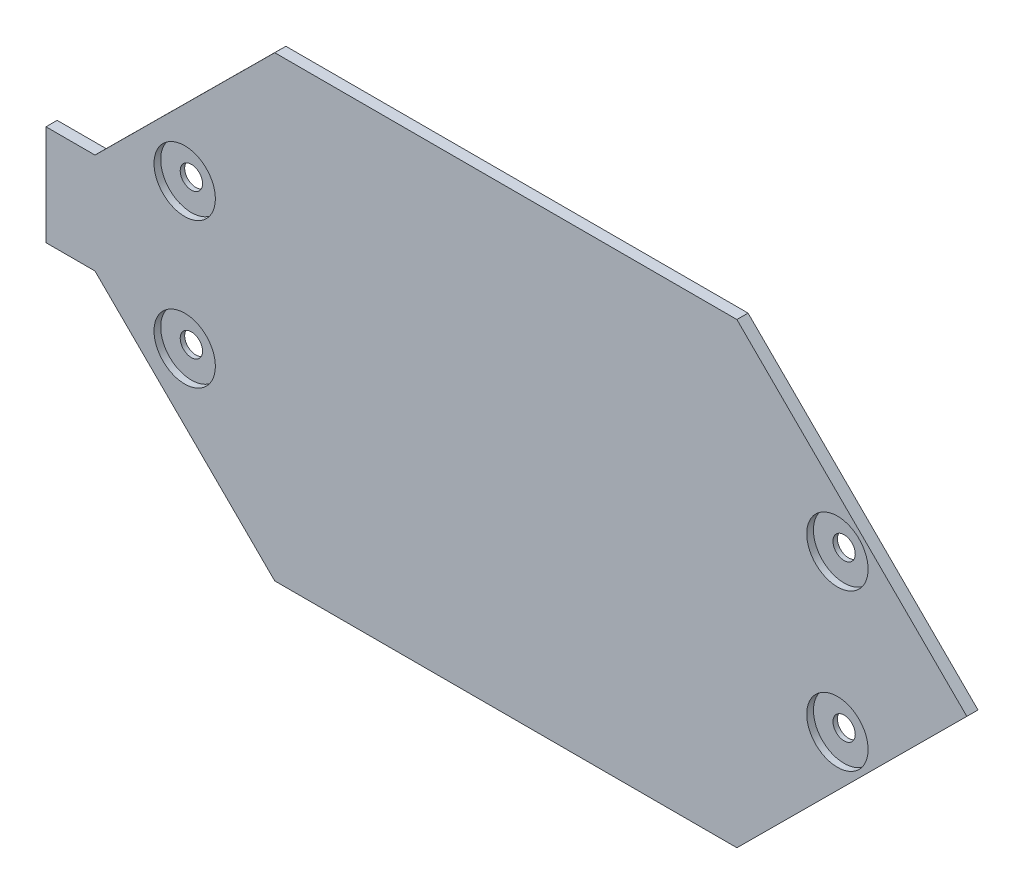
SolidWorks part; units mm, degrees
ref_plane "Front" through (0, 0, 0) normal (0, 0, 1) x (1, 0, 0)
ref_plane "Top" through (0, 0, 0) normal (0, 1, 0) x (1, 0, 0)
ref_plane "Right" through (0, 0, 0) normal (1, 0, 0) x (0, 0, -1)
sketch "Sketch2" plane through (0, 0, 0) normal (0, 0, 1) x (1, 0, 0)
  line L1 (16.46, 48.53) -> (32.57, 32.53)
  line L2 (32.57, 32.53) -> (73.99, 32.53)
  line L3 (73.99, 32.53) -> (94.6, 53.03)
  line L4 (94.6, 53.03) -> (73.99, 73.53)
  line L5 (73.99, 73.53) -> (32.57, 73.53)
  line L6 (32.57, 73.53) -> (16.46, 57.53)
  line L11 (12.07, 57.53) -> (12.07, 48.53)
  line L12 (12.07, 48.53) -> (16.46, 48.53)
  line L13 (12.07, 57.53) -> (16.46, 57.53)
  circle A0 centre (24.5, 59.53) radius 1
  circle A1 centre (24.5, 46.53) radius 1
  circle A2 centre (83, 60.03) radius 1
  circle A3 centre (83, 46.03) radius 1
  point P0 (16.46, 57.53)
  point P1 (32.57, 73.53)
  point P2 (73.99, 73.53)
  point P3 (94.6, 53.03)
  point P4 (73.99, 32.53)
  point P5 (32.57, 32.53)
  point P6 (16.46, 48.53)
  point P24 (12.07, 57.53)
  point P27 (12.07, 48.53)
extrude "Boss-Extrude1" add sketch "Sketch2" along normal blind 1
sketch "Sketch3" plane through (0, 0, 0) normal (0, 0, 1) x (1, 0, 0)
  circle A0 centre (24.5, 59.53) radius 2.75
  circle A1 centre (24.5, 46.53) radius 2.75
  circle A2 centre (83, 60.03) radius 2.75
  circle A3 centre (83, 46.03) radius 2.75
extrude "Cut-Extrude1" cut sketch "Sketch3" against normal blind 0.6 from surface at 1 starting at face at (84, 60.03, 1)
